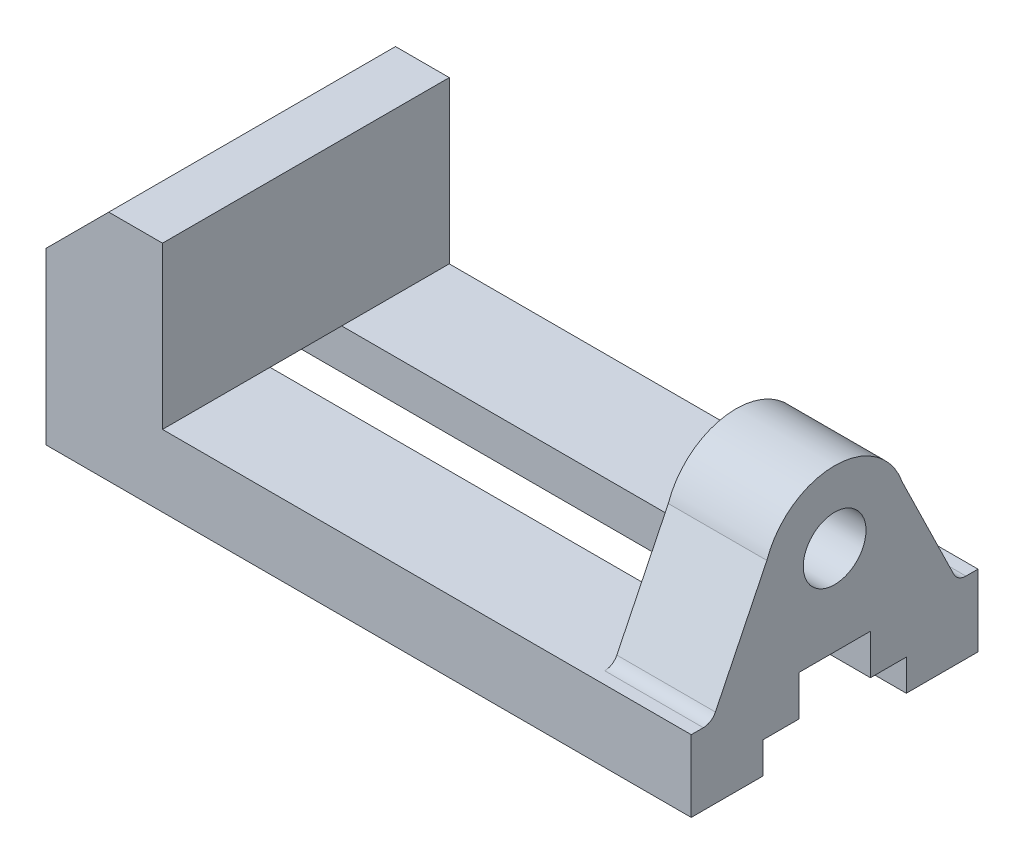
SolidWorks part; units mm, degrees
ref_plane "Ön Düzlem" through (0, 0, 0) normal (0, 0, 1) x (1, 0, 0)
ref_plane "Üst Düzlem" through (0, 0, 0) normal (0, 1, 0) x (1, 0, 0)
ref_plane "Sağ Düzlem" through (0, 0, 0) normal (1, 0, 0) x (0, 0, -1)
sketch "Çizim1" plane through (0, 0, 0) normal (0, 1, 0) x (1, 0, 0)
  line L0 (-72.7302, -32.0552) -> (71.2698, -32.0552)
  line L1 (71.2698, -32.0552) -> (71.2698, 31.9448)
  line L2 (71.2698, 31.9448) -> (-72.7302, 31.9448)
  line L3 (-72.7302, 31.9448) -> (-72.7302, -32.0552)
extrude "Yükseklik-Ekstrüzyon1" add sketch "Çizim1" along normal blind 16
sketch "Çizim2" plane through (71.2698, 0, 0) normal (1, 0, 0) x (0, 0, -1)
  line L0 (-16.0552, 0) -> (15.9448, 0)
  line L1 (-32.0552, 0) -> (31.9448, 0) construction
  line L2 (-16.0552, 0) -> (-16.0552, 7)
  line L3 (-16.0552, 7) -> (-8.0552, 7)
  line L4 (-8.0552, 7) -> (-8.0552, 16)
  line L5 (-32.0552, 16) -> (31.9448, 16) construction
  line L6 (-8.0552, 16) -> (7.9448, 16)
  line L7 (7.9448, 16) -> (7.9448, 7)
  line L8 (7.9448, 7) -> (15.9448, 7)
  line L9 (15.9448, 7) -> (15.9448, 0)
extrude "Kes-Ekstrüzyon1" cut sketch "Çizim2" against normal blind 187
sketch "Çizim3" plane through (0, 16, 0) normal (0, 1, 0) x (1, 0, 0)
  line L0 (71.2698, 31.9448) -> (49.2698, 31.9448)
  line L1 (71.2698, 31.9448) -> (-72.7302, 31.9448) construction
  line L2 (49.2698, 31.9448) -> (49.2698, -32.0552)
  line L3 (-72.7302, -32.0552) -> (71.2698, -32.0552) construction
  line L4 (49.2698, -32.0552) -> (71.2698, -32.0552)
  line L5 (71.2698, -32.0552) -> (71.2698, 31.9448)
extrude "Yükseklik-Ekstrüzyon2" add sketch "Çizim3" along normal blind 36
sketch "Çizim7" plane through (0, 16, 0) normal (0, 1, 0) x (1, 0, 0)
  line L0 (-72.7302, 31.9448) -> (-46.7302, 31.9448)
  line L1 (49.2698, 31.9448) -> (-72.7302, 31.9448) construction
  line L2 (-46.7302, 31.9448) -> (-46.7302, -32.0552)
  line L3 (-72.7302, -32.0552) -> (49.2698, -32.0552) construction
  line L4 (-46.7302, -32.0552) -> (-72.7302, -32.0552)
  line L5 (-72.7302, -32.0552) -> (-72.7302, 31.9448)
extrude "Yükseklik-Ekstrüzyon3" add sketch "Çizim7" along normal blind 36
chamfer "Pah2" distance 14 angle 45 1 edges at (-72.7302, 52, 0.0552)
sketch "Çizim8" plane through (71.2698, 0, 0) normal (1, 0, 0) x (0, 0, -1)
  line L0 (27.3716, 16) -> (31.9448, 16)
  line L1 (31.9448, 52) -> (31.9448, 0) construction
  line L2 (-27.482, 16) -> (-32.0552, 16)
  line L3 (-32.0552, 16) -> (-32.0552, 52)
  line L4 (-32.0552, 52) -> (31.9448, 52)
  line L5 (31.9448, 52) -> (31.9448, 16)
  line L6 (27.3716, 16) -> (15.0654, 41.2316)
  line L8 (-27.482, 16) -> (-15.1757, 41.2316)
  arc A0 (15.0654, 41.2316) -> (-15.1757, 41.2316) centre (-0.0552, 36) ccw
  line M14 (31.9448, 0) -> (31.9448, 52)
  line M15 (31.9448, 52) -> (-32.0552, 52)
  line M16 (-32.0552, 52) -> (-32.0552, 0)
  dimension "D2" = 32
extrude "Kes-Ekstrüzyon2" cut sketch "Çizim8" against normal up to next contours A0 L4 L2 L8 M16 | A0 L6 L0 M14 M15
fillet "Radyus1" radius 3 2 edges at (60.2698, 16, -27.3716) (60.2698, 16, 27.482)
hole_wizard "M16x2.0 Dişli Delik1" positions "3B Çizim1" profile "Çizim9" tap size "M16x2.0" standard "ANSI Metrik" end condition up to next
sketch3d "3B Çizim1"
  line L0 (49.2698, 36, 0.0552) -> (71.2698, 36, 0.0552) construction
  point P0 (71.2698, 36, 0.0552)
cosmetic thread "Delik Dişi1" parameters "D2"=16
sketch "Çizim9" plane through (71.2698, 36, 0.0552) normal (0, 1, 0) x (0, 0, -1)
  line L0 (0, 0) -> (0, 22)
  line L1 (0, 22) -> (7, 22)
  line L2 (7, 22) -> (7, 0)
  line L5 (7, 0) -> (0, 0)
  line L11 (0, -6.35) -> (0, 107.95) construction
  dimension "Thru Tap Drill Dia." = 14
  dimension "Thru Tap Drill Depth" = 22
hole_wizard "M6x1.0 Dişli Delik1" positions "3B Çizim2" profile "Çizim10" tap size "M6x1.0" standard "ANSI Metrik"
sketch3d "3B Çizim2"
  line L0 (-72.7302, 0, -31.9448) -> (-72.7302, 0, -15.9448) construction
  line L1 (-72.7302, 7, -15.9448) -> (71.2698, 7, -15.9448) construction
  line L2 (71.2698, 0, -31.9448) -> (-72.7302, 0, -31.9448) construction
  line L3 (71.2698, 0, -15.9448) -> (71.2698, 0, -31.9448) construction
  line L4 (-72.7302, 0, 32.0552) -> (71.2698, 0, 32.0552) construction
  line L5 (71.2698, 0, 32.0552) -> (71.2698, 0, 16.0552) construction
  line L6 (-72.7302, 0, 16.0552) -> (-72.7302, 0, 32.0552) construction
  point P0 (-36.7302, 0, -23.0863)
  point P2 (-36.7302, 0, 22.0552)
  point P4 (35.2698, 0, 22.0552)
  point P6 (35.2698, 0, -21.9448)
  dimension "D1" = 36
  dimension "D2" = 10
  dimension "D3" = 10
  dimension "D4" = 36
  dimension "D5" = 10
  dimension "D6" = 36
  dimension "D7" = 10
  dimension "D8" = 36
sketch "Çizim10" plane through (-36.7302, 0, -23.0863) normal (1, 0, 0) x (0, 0, -1)
  line L0 (0, 0) -> (0, 13.5022)
  line L1 (0, 13.5022) -> (2.5, 12)
  line L2 (2.5, 12) -> (2.5, 0)
  line L5 (2.5, 0) -> (0, 0)
  line L10 (0, 13.5022) -> (-2.5, 12) construction
  line L11 (0, -6.35) -> (0, 107.95) construction
  dimension "Tap Drill Dia." = 5
  dimension "Tap Drill Depth" = 12
  dimension "Drill Angle" = 118
cosmetic thread "Delik Dişi2" parameters "D1"=10, "D2"=6
cosmetic thread "Delik Dişi3" parameters "D1"=10, "D2"=6
cosmetic thread "Delik Dişi4" parameters "D1"=10, "D2"=6
cosmetic thread "Delik Dişi5" parameters "D1"=10, "D2"=6
